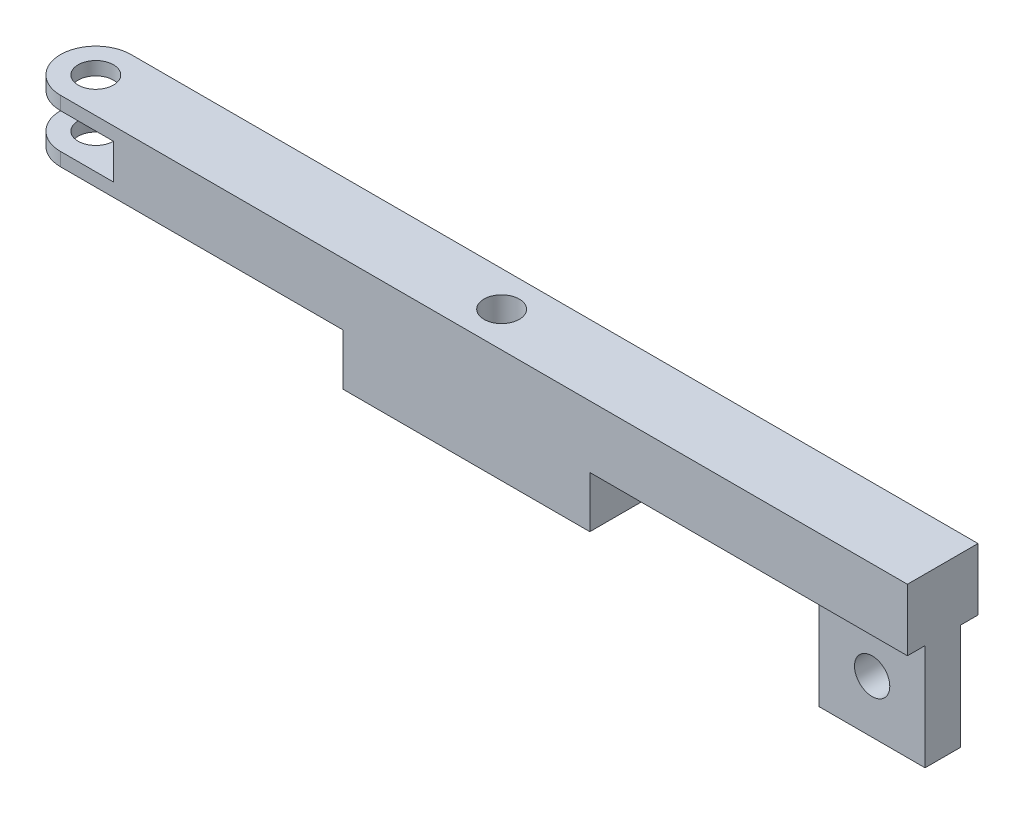
SolidWorks part; units mm, degrees
ref_plane "Front Plane" through (0, 0, 0) normal (0, 0, 1) x (1, 0, 0)
ref_plane "Top Plane" through (0, 0, 0) normal (0, 1, 0) x (1, 0, 0)
ref_plane "Right Plane" through (0, 0, 0) normal (1, 0, 0) x (0, 0, -1)
sketch "Sketch1" plane through (0, 0, 0) normal (0, 0, 1) x (1, 0, 0)
  line L0 (-100, 0) -> (0, 0) construction
  line L1 (-125, -8.78) -> (125, -8.78)
  line L2 (-125, -8.78) -> (-125, -5)
  line L3 (-125, 8.78) -> (125, 8.78)
  line L4 (125, -8.78) -> (125, 8.78)
  line L5 (-125, -8.78) -> (125, 8.78) construction
  line L6 (-125, 8.78) -> (125, -8.78) construction
  line L7 (-125, 5) -> (-125, 8.78)
  line L8 (-125, -5) -> (-100, -5)
  line L10 (-125, 5) -> (-100, 5)
  line L11 (-100, -5) -> (-100, 5)
  point P0 (0, 0)
  dimension "D1" = 8.78
  dimension "D2" = 250
extrude "Boss-Extrude1" add sketch "Sketch1" along normal blind 20
sketch "Sketch2" plane through (0, 5, 0) normal (0, -1, 0) x (1, 0, 0)
  line L0 (-115, 20) -> (-115, 22.0291)
  line L1 (-125, 20) -> (-125, 0) construction
  line L2 (-115, 22.0291) -> (-130, 22.0291)
  line L3 (-130, 22.0291) -> (-130, -2.1931)
  line L4 (-130, -2.1931) -> (-115, -2.1931)
  line L5 (-115, -2.1931) -> (-115, 0)
  line L6 (0, 0) -> (0, 20) construction
  line L7 (-125, 20) -> (125, 20) construction
  circle A0 centre (-115, 10) radius 5
  arc A1 (-115, 20) -> (-115, 0) centre (-115, 10) ccw
  circle A2 centre (0, 10) radius 5
  dimension "D2" = 10
  dimension "D3" = 5
  dimension "D4" = 10
  dimension "D1" = 10
extrude "Cut-Extrude1" cut sketch "Sketch2" against normal mid plane 40
sketch "Sketch3" plane through (0, -8.78, 0) normal (0, -1, 0) x (1, 0, 0)
  line L0 (-115, 20) -> (125, 20) construction
  line L1 (-35, 0) -> (35, 0)
  line L2 (-35, 0) -> (-35, 20)
  line L3 (-35, 20) -> (35, 20)
  line L4 (35, 0) -> (35, 20)
  line L5 (-35, 0) -> (35, 20) construction
  line L6 (-35, 20) -> (35, 0) construction
  circle A0 centre (0, 10) radius 5
  dimension "D1" = 70
extrude "Boss-Extrude2" add sketch "Sketch3" along normal blind 14.55
sketch "Sketch4" plane through (0, -8.78, 0) normal (0, -1, 0) x (1, 0, 0)
  line L0 (125, 20) -> (125, 0) construction
  line L1 (125, 5) -> (95, 5)
  line L2 (125, 5) -> (125, 15)
  line L3 (125, 15) -> (95, 15)
  line L4 (95, 5) -> (95, 15)
  line L5 (35, 0) -> (125, 0) construction
  point P6 (110, 5)
  dimension "D1" = 10
  dimension "D2" = 5
  dimension "D3" = 30
extrude "Boss-Extrude3" add sketch "Sketch4" along normal blind 30
sketch "Sketch5" plane through (0, 0, 15) normal (0, 0, 1) x (1, 0, 0)
  line L0 (95, -23.78) -> (125, -23.78) construction
  line L1 (95, -38.78) -> (95, -8.78) construction
  line L2 (125, -38.78) -> (125, -8.78) construction
  circle A0 centre (110, -23.78) radius 5
  dimension "D1" = 10
extrude "Cut-Extrude2" cut sketch "Sketch5" against normal blind 20
